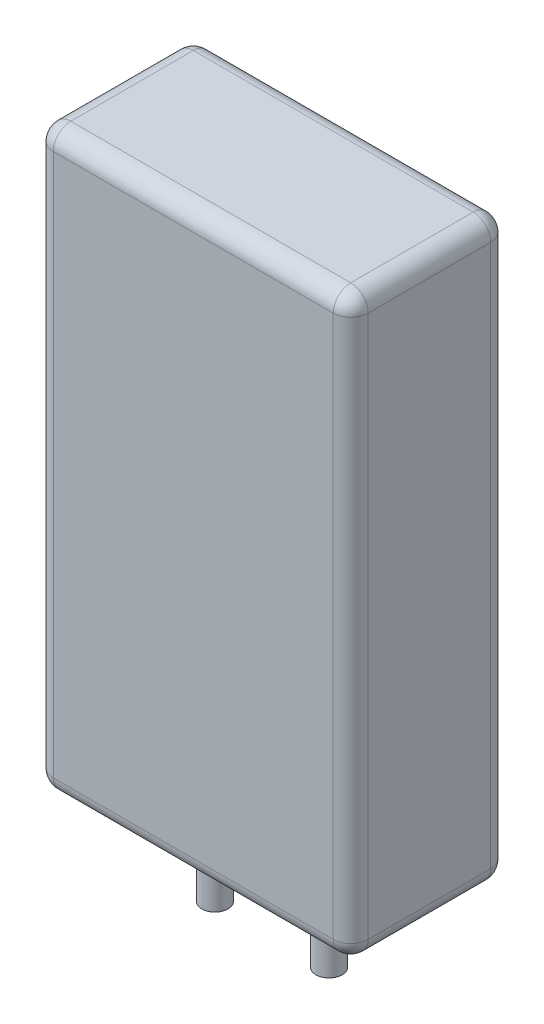
SolidWorks part; units mm, degrees
ref_plane "Plan de face" through (0, 0, 0) normal (0, 0, 1) x (1, 0, 0)
ref_plane "Plan de dessus" through (0, 0, 0) normal (0, 1, 0) x (1, 0, 0)
ref_plane "Plan de droite" through (0, 0, 0) normal (1, 0, 0) x (0, 0, -1)
sketch "Esquisse1" plane through (0, 0, 0) normal (0, 0, 1) x (1, 0, 0)
  line L1 (-18.4863, 43.7355) -> (17.5137, 43.7355)
  line L2 (-18.4863, 43.7355) -> (-18.4863, -22.2645)
  line L3 (-18.4863, -22.2645) -> (17.5137, -22.2645)
  line L4 (17.5137, 43.7355) -> (17.5137, -22.2645)
  dimension "D1" = 36
  dimension "D2" = 66
extrude "Boss.-Extru.1" add sketch "Esquisse1" along normal blind 18
fillet "Congé1" radius 2 12 edges at (-0.4863, -22.2645, 0) (-18.4863, -22.2645, 9) (-18.4863, 10.7355, 0) (-18.4863, 43.7355, 9) (-0.4863, 43.7355, 0) (-0.4863, 43.7355, 18) (-0.4863, -22.2645, 18) (-18.4863, 10.7355, 18) (17.5137, -22.2645, 9) (17.5137, 10.7355, 18) (17.5137, 43.7355, 9) (17.5137, 10.7355, 0)
sketch "Esquisse2" plane through (0, -22.2645, 0) normal (0, -1, 0) x (1, 0, 0)
  line L0 (-0.4863, 2) -> (-0.4863, 16) construction
  line L1 (-16.4863, 2) -> (15.5137, 2) construction
  line L3 (15.5137, 16) -> (-16.4863, 16) construction
  circle A0 centre (-7.0087, 9) radius 1.5
  circle A1 centre (6.0361, 9) radius 1.5
extrude "Boss.-Extru.2" add sketch "Esquisse2" along normal blind 10
sketch "Esquisse3" plane through (0, -22.2645, 0) normal (0, -1, 0) x (1, 0, 0)
  circle A1 centre (6.0361, 9) radius 1.5 construction
  circle A8 centre (6.0361, 9) radius 1.5
  circle A9 centre (-7.0087, 9) radius 1.5 construction
  circle A10 centre (-7.0087, 9) radius 1.5
  circle A11 centre (-7.0087, 9) radius 2
  circle A12 centre (6.0361, 9) radius 2
  dimension "D1" = 0.5
extrude "Boss.-Extru.3" add sketch "Esquisse3" along normal blind 5
